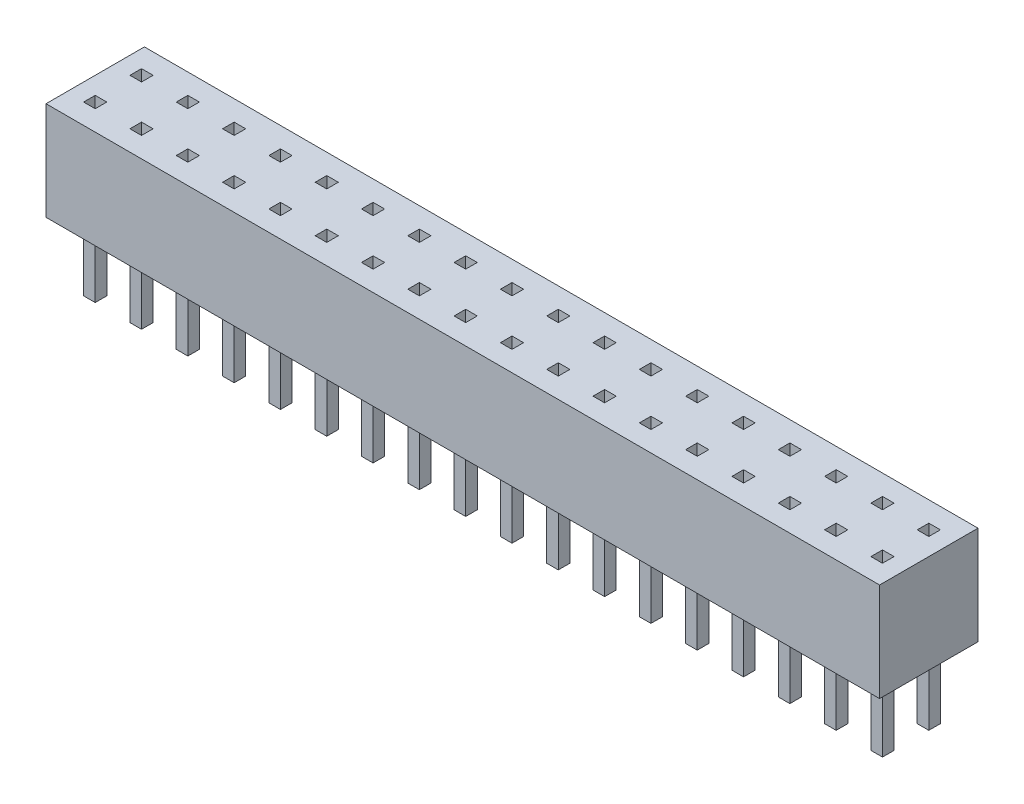
SolidWorks part; units mm, degrees
ref_plane "Front Plane" through (0, 0, 0) normal (0, 0, 1) x (1, 0, 0)
ref_plane "Top Plane" through (0, 0, 0) normal (0, 1, 0) x (1, 0, 0)
ref_plane "Right Plane" through (0, 0, 0) normal (1, 0, 0) x (0, 0, -1)
sketch "Sketch1" plane through (0, 0, 0) normal (0, 1, 0) x (1, 0, 0)
  line L1 (0, 0) -> (36, 0)
  line L2 (0, 0) -> (0, -4.25)
  line L3 (0, -4.25) -> (36, -4.25)
  line L4 (36, 0) -> (36, -4.25)
extrude "Boss-Extrude1" add sketch "Sketch1" along normal blind 4.25
sketch "Sketch3" plane through (0, 0, 0) normal (0, -1, 0) x (1, 0, 0)
  line L0 (2.75, 0.875) -> (3.25, 0.875)
  line L1 (0.75, 0.875) -> (1.25, 0.875)
  line L2 (0.75, 0.875) -> (0.75, 1.375)
  line L3 (0.75, 1.375) -> (1.25, 1.375)
  line L4 (1.25, 0.875) -> (1.25, 1.375)
  line L5 (2.75, 0.875) -> (2.75, 1.375)
  line L6 (2.75, 1.375) -> (3.25, 1.375)
  line L7 (3.25, 0.875) -> (3.25, 1.375)
  line L8 (4.75, 0.875) -> (5.25, 0.875)
  line L9 (4.75, 0.875) -> (4.75, 1.375)
  line L10 (4.75, 1.375) -> (5.25, 1.375)
  line L11 (5.25, 0.875) -> (5.25, 1.375)
  line L12 (6.75, 0.875) -> (7.25, 0.875)
  line L13 (6.75, 0.875) -> (6.75, 1.375)
  line L14 (6.75, 1.375) -> (7.25, 1.375)
  line L15 (7.25, 0.875) -> (7.25, 1.375)
  line L16 (8.75, 0.875) -> (9.25, 0.875)
  line L17 (8.75, 0.875) -> (8.75, 1.375)
  line L18 (8.75, 1.375) -> (9.25, 1.375)
  line L19 (9.25, 0.875) -> (9.25, 1.375)
  line L20 (10.75, 0.875) -> (11.25, 0.875)
  line L21 (10.75, 0.875) -> (10.75, 1.375)
  line L22 (10.75, 1.375) -> (11.25, 1.375)
  line L23 (11.25, 0.875) -> (11.25, 1.375)
  line L24 (12.75, 0.875) -> (13.25, 0.875)
  line L25 (12.75, 0.875) -> (12.75, 1.375)
  line L26 (12.75, 1.375) -> (13.25, 1.375)
  line L27 (13.25, 0.875) -> (13.25, 1.375)
  line L28 (14.75, 0.875) -> (15.25, 0.875)
  line L29 (14.75, 0.875) -> (14.75, 1.375)
  line L30 (14.75, 1.375) -> (15.25, 1.375)
  line L31 (15.25, 0.875) -> (15.25, 1.375)
  line L32 (16.75, 0.875) -> (17.25, 0.875)
  line L33 (16.75, 0.875) -> (16.75, 1.375)
  line L34 (16.75, 1.375) -> (17.25, 1.375)
  line L35 (17.25, 0.875) -> (17.25, 1.375)
  line L36 (18.75, 0.875) -> (19.25, 0.875)
  line L37 (18.75, 0.875) -> (18.75, 1.375)
  line L38 (18.75, 1.375) -> (19.25, 1.375)
  line L39 (19.25, 0.875) -> (19.25, 1.375)
  line L40 (20.75, 0.875) -> (21.25, 0.875)
  line L41 (20.75, 0.875) -> (20.75, 1.375)
  line L42 (20.75, 1.375) -> (21.25, 1.375)
  line L43 (21.25, 0.875) -> (21.25, 1.375)
  line L44 (22.75, 0.875) -> (23.25, 0.875)
  line L45 (22.75, 0.875) -> (22.75, 1.375)
  line L46 (22.75, 1.375) -> (23.25, 1.375)
  line L47 (23.25, 0.875) -> (23.25, 1.375)
  line L48 (24.75, 0.875) -> (25.25, 0.875)
  line L49 (24.75, 0.875) -> (24.75, 1.375)
  line L50 (24.75, 1.375) -> (25.25, 1.375)
  line L51 (25.25, 0.875) -> (25.25, 1.375)
  line L52 (26.75, 0.875) -> (27.25, 0.875)
  line L53 (26.75, 0.875) -> (26.75, 1.375)
  line L54 (26.75, 1.375) -> (27.25, 1.375)
  line L55 (27.25, 0.875) -> (27.25, 1.375)
  line L56 (28.75, 0.875) -> (29.25, 0.875)
  line L57 (28.75, 0.875) -> (28.75, 1.375)
  line L58 (28.75, 1.375) -> (29.25, 1.375)
  line L59 (29.25, 0.875) -> (29.25, 1.375)
  line L60 (30.75, 0.875) -> (31.25, 0.875)
  line L61 (30.75, 0.875) -> (30.75, 1.375)
  line L62 (30.75, 1.375) -> (31.25, 1.375)
  line L63 (31.25, 0.875) -> (31.25, 1.375)
  line L64 (32.75, 0.875) -> (33.25, 0.875)
  line L65 (32.75, 0.875) -> (32.75, 1.375)
  line L66 (32.75, 1.375) -> (33.25, 1.375)
  line L67 (33.25, 0.875) -> (33.25, 1.375)
  line L68 (34.75, 0.875) -> (35.25, 0.875)
  line L69 (34.75, 0.875) -> (34.75, 1.375)
  line L70 (34.75, 1.375) -> (35.25, 1.375)
  line L71 (35.25, 0.875) -> (35.25, 1.375)
  line L72 (0.75, 2.875) -> (1.25, 2.875)
  line L73 (0.75, 2.875) -> (0.75, 3.375)
  line L74 (0.75, 3.375) -> (1.25, 3.375)
  line L75 (1.25, 2.875) -> (1.25, 3.375)
  line L76 (2.75, 2.875) -> (3.25, 2.875)
  line L77 (2.75, 2.875) -> (2.75, 3.375)
  line L78 (2.75, 3.375) -> (3.25, 3.375)
  line L79 (3.25, 2.875) -> (3.25, 3.375)
  line L80 (4.75, 2.875) -> (5.25, 2.875)
  line L81 (4.75, 2.875) -> (4.75, 3.375)
  line L82 (4.75, 3.375) -> (5.25, 3.375)
  line L83 (5.25, 2.875) -> (5.25, 3.375)
  line L84 (6.75, 2.875) -> (7.25, 2.875)
  line L85 (6.75, 2.875) -> (6.75, 3.375)
  line L86 (6.75, 3.375) -> (7.25, 3.375)
  line L87 (7.25, 2.875) -> (7.25, 3.375)
  line L88 (8.75, 2.875) -> (9.25, 2.875)
  line L89 (8.75, 2.875) -> (8.75, 3.375)
  line L90 (8.75, 3.375) -> (9.25, 3.375)
  line L91 (9.25, 2.875) -> (9.25, 3.375)
  line L92 (10.75, 2.875) -> (11.25, 2.875)
  line L93 (10.75, 2.875) -> (10.75, 3.375)
  line L94 (10.75, 3.375) -> (11.25, 3.375)
  line L95 (11.25, 2.875) -> (11.25, 3.375)
  line L96 (12.75, 2.875) -> (13.25, 2.875)
  line L97 (12.75, 2.875) -> (12.75, 3.375)
  line L98 (12.75, 3.375) -> (13.25, 3.375)
  line L99 (13.25, 2.875) -> (13.25, 3.375)
  line L100 (14.75, 2.875) -> (15.25, 2.875)
  line L101 (14.75, 2.875) -> (14.75, 3.375)
  line L102 (14.75, 3.375) -> (15.25, 3.375)
  line L103 (15.25, 2.875) -> (15.25, 3.375)
  line L104 (16.75, 2.875) -> (17.25, 2.875)
  line L105 (16.75, 2.875) -> (16.75, 3.375)
  line L106 (16.75, 3.375) -> (17.25, 3.375)
  line L107 (17.25, 2.875) -> (17.25, 3.375)
  line L108 (18.75, 2.875) -> (19.25, 2.875)
  line L109 (18.75, 2.875) -> (18.75, 3.375)
  line L110 (18.75, 3.375) -> (19.25, 3.375)
  line L111 (19.25, 2.875) -> (19.25, 3.375)
  line L112 (20.75, 2.875) -> (21.25, 2.875)
  line L113 (20.75, 2.875) -> (20.75, 3.375)
  line L114 (20.75, 3.375) -> (21.25, 3.375)
  line L115 (21.25, 2.875) -> (21.25, 3.375)
  line L116 (22.75, 2.875) -> (23.25, 2.875)
  line L117 (22.75, 2.875) -> (22.75, 3.375)
  line L118 (22.75, 3.375) -> (23.25, 3.375)
  line L119 (23.25, 2.875) -> (23.25, 3.375)
  line L120 (24.75, 2.875) -> (25.25, 2.875)
  line L121 (24.75, 2.875) -> (24.75, 3.375)
  line L122 (24.75, 3.375) -> (25.25, 3.375)
  line L123 (25.25, 2.875) -> (25.25, 3.375)
  line L124 (26.75, 2.875) -> (27.25, 2.875)
  line L125 (26.75, 2.875) -> (26.75, 3.375)
  line L126 (26.75, 3.375) -> (27.25, 3.375)
  line L127 (27.25, 2.875) -> (27.25, 3.375)
  line L128 (28.75, 2.875) -> (29.25, 2.875)
  line L129 (28.75, 2.875) -> (28.75, 3.375)
  line L130 (28.75, 3.375) -> (29.25, 3.375)
  line L131 (29.25, 2.875) -> (29.25, 3.375)
  line L132 (30.75, 2.875) -> (31.25, 2.875)
  line L133 (30.75, 2.875) -> (30.75, 3.375)
  line L134 (30.75, 3.375) -> (31.25, 3.375)
  line L135 (31.25, 2.875) -> (31.25, 3.375)
  line L136 (32.75, 2.875) -> (33.25, 2.875)
  line L138 (32.75, 2.875) -> (32.75, 3.375)
  line L140 (32.75, 3.375) -> (33.25, 3.375)
  line L142 (33.25, 2.875) -> (33.25, 3.375)
  line L145 (34.75, 2.875) -> (35.25, 2.875)
  line L146 (34.75, 2.875) -> (34.75, 3.375)
  line L147 (34.75, 3.375) -> (35.25, 3.375)
  line L148 (35.25, 2.875) -> (35.25, 3.375)
  dimension "D2" = 2
  dimension "D1" = 18
extrude "Boss-Extrude2" add sketch "Sketch3" along normal blind 3
sketch "Sketch4" plane through (0, 4.25, 0) normal (0, 1, 0) x (-1, 0, 0)
  line L0 (-33.25, 0.875) -> (-32.75, 0.875)
  line L1 (-35.25, 0.875) -> (-34.75, 0.875)
  line L2 (-35.25, 0.875) -> (-35.25, 1.375)
  line L3 (-35.25, 1.375) -> (-34.75, 1.375)
  line L4 (-34.75, 0.875) -> (-34.75, 1.375)
  line L5 (-33.25, 0.875) -> (-33.25, 1.375)
  line L6 (-33.25, 1.375) -> (-32.75, 1.375)
  line L7 (-32.75, 0.875) -> (-32.75, 1.375)
  line L8 (-31.25, 0.875) -> (-30.75, 0.875)
  line L9 (-31.25, 0.875) -> (-31.25, 1.375)
  line L10 (-31.25, 1.375) -> (-30.75, 1.375)
  line L11 (-30.75, 0.875) -> (-30.75, 1.375)
  line L12 (-29.25, 0.875) -> (-28.75, 0.875)
  line L13 (-29.25, 0.875) -> (-29.25, 1.375)
  line L14 (-29.25, 1.375) -> (-28.75, 1.375)
  line L15 (-28.75, 0.875) -> (-28.75, 1.375)
  line L16 (-27.25, 0.875) -> (-26.75, 0.875)
  line L17 (-27.25, 0.875) -> (-27.25, 1.375)
  line L18 (-27.25, 1.375) -> (-26.75, 1.375)
  line L19 (-26.75, 0.875) -> (-26.75, 1.375)
  line L20 (-25.25, 0.875) -> (-24.75, 0.875)
  line L21 (-25.25, 0.875) -> (-25.25, 1.375)
  line L22 (-25.25, 1.375) -> (-24.75, 1.375)
  line L23 (-24.75, 0.875) -> (-24.75, 1.375)
  line L24 (-23.25, 0.875) -> (-22.75, 0.875)
  line L25 (-23.25, 0.875) -> (-23.25, 1.375)
  line L26 (-23.25, 1.375) -> (-22.75, 1.375)
  line L27 (-22.75, 0.875) -> (-22.75, 1.375)
  line L28 (-21.25, 0.875) -> (-20.75, 0.875)
  line L29 (-21.25, 0.875) -> (-21.25, 1.375)
  line L30 (-21.25, 1.375) -> (-20.75, 1.375)
  line L31 (-20.75, 0.875) -> (-20.75, 1.375)
  line L32 (-19.25, 0.875) -> (-18.75, 0.875)
  line L33 (-19.25, 0.875) -> (-19.25, 1.375)
  line L34 (-19.25, 1.375) -> (-18.75, 1.375)
  line L35 (-18.75, 0.875) -> (-18.75, 1.375)
  line L36 (-17.25, 0.875) -> (-16.75, 0.875)
  line L37 (-17.25, 0.875) -> (-17.25, 1.375)
  line L38 (-17.25, 1.375) -> (-16.75, 1.375)
  line L39 (-16.75, 0.875) -> (-16.75, 1.375)
  line L40 (-15.25, 0.875) -> (-14.75, 0.875)
  line L41 (-15.25, 0.875) -> (-15.25, 1.375)
  line L42 (-15.25, 1.375) -> (-14.75, 1.375)
  line L43 (-14.75, 0.875) -> (-14.75, 1.375)
  line L44 (-13.25, 0.875) -> (-12.75, 0.875)
  line L45 (-13.25, 0.875) -> (-13.25, 1.375)
  line L46 (-13.25, 1.375) -> (-12.75, 1.375)
  line L47 (-12.75, 0.875) -> (-12.75, 1.375)
  line L48 (-11.25, 0.875) -> (-10.75, 0.875)
  line L49 (-11.25, 0.875) -> (-11.25, 1.375)
  line L50 (-11.25, 1.375) -> (-10.75, 1.375)
  line L51 (-10.75, 0.875) -> (-10.75, 1.375)
  line L52 (-9.25, 0.875) -> (-8.75, 0.875)
  line L53 (-9.25, 0.875) -> (-9.25, 1.375)
  line L54 (-9.25, 1.375) -> (-8.75, 1.375)
  line L55 (-8.75, 0.875) -> (-8.75, 1.375)
  line L56 (-7.25, 0.875) -> (-6.75, 0.875)
  line L57 (-7.25, 0.875) -> (-7.25, 1.375)
  line L58 (-7.25, 1.375) -> (-6.75, 1.375)
  line L59 (-6.75, 0.875) -> (-6.75, 1.375)
  line L60 (-5.25, 0.875) -> (-4.75, 0.875)
  line L61 (-5.25, 0.875) -> (-5.25, 1.375)
  line L62 (-5.25, 1.375) -> (-4.75, 1.375)
  line L63 (-4.75, 0.875) -> (-4.75, 1.375)
  line L64 (-3.25, 0.875) -> (-2.75, 0.875)
  line L65 (-3.25, 0.875) -> (-3.25, 1.375)
  line L66 (-3.25, 1.375) -> (-2.75, 1.375)
  line L67 (-2.75, 0.875) -> (-2.75, 1.375)
  line L68 (-1.25, 0.875) -> (-0.75, 0.875)
  line L69 (-1.25, 0.875) -> (-1.25, 1.375)
  line L70 (-1.25, 1.375) -> (-0.75, 1.375)
  line L71 (-0.75, 0.875) -> (-0.75, 1.375)
  line L72 (-35.25, 2.875) -> (-34.75, 2.875)
  line L73 (-35.25, 2.875) -> (-35.25, 3.375)
  line L74 (-35.25, 3.375) -> (-34.75, 3.375)
  line L75 (-34.75, 2.875) -> (-34.75, 3.375)
  line L76 (-33.25, 2.875) -> (-32.75, 2.875)
  line L77 (-33.25, 2.875) -> (-33.25, 3.375)
  line L78 (-33.25, 3.375) -> (-32.75, 3.375)
  line L79 (-32.75, 2.875) -> (-32.75, 3.375)
  line L80 (-31.25, 2.875) -> (-30.75, 2.875)
  line L81 (-31.25, 2.875) -> (-31.25, 3.375)
  line L82 (-31.25, 3.375) -> (-30.75, 3.375)
  line L83 (-30.75, 2.875) -> (-30.75, 3.375)
  line L84 (-29.25, 2.875) -> (-28.75, 2.875)
  line L85 (-29.25, 2.875) -> (-29.25, 3.375)
  line L86 (-29.25, 3.375) -> (-28.75, 3.375)
  line L87 (-28.75, 2.875) -> (-28.75, 3.375)
  line L88 (-27.25, 2.875) -> (-26.75, 2.875)
  line L89 (-27.25, 2.875) -> (-27.25, 3.375)
  line L90 (-27.25, 3.375) -> (-26.75, 3.375)
  line L91 (-26.75, 2.875) -> (-26.75, 3.375)
  line L92 (-25.25, 2.875) -> (-24.75, 2.875)
  line L93 (-25.25, 2.875) -> (-25.25, 3.375)
  line L94 (-25.25, 3.375) -> (-24.75, 3.375)
  line L95 (-24.75, 2.875) -> (-24.75, 3.375)
  line L96 (-23.25, 2.875) -> (-22.75, 2.875)
  line L97 (-23.25, 2.875) -> (-23.25, 3.375)
  line L98 (-23.25, 3.375) -> (-22.75, 3.375)
  line L99 (-22.75, 2.875) -> (-22.75, 3.375)
  line L100 (-21.25, 2.875) -> (-20.75, 2.875)
  line L101 (-21.25, 2.875) -> (-21.25, 3.375)
  line L102 (-21.25, 3.375) -> (-20.75, 3.375)
  line L103 (-20.75, 2.875) -> (-20.75, 3.375)
  line L104 (-19.25, 2.875) -> (-18.75, 2.875)
  line L105 (-19.25, 2.875) -> (-19.25, 3.375)
  line L106 (-19.25, 3.375) -> (-18.75, 3.375)
  line L107 (-18.75, 2.875) -> (-18.75, 3.375)
  line L108 (-17.25, 2.875) -> (-16.75, 2.875)
  line L109 (-17.25, 2.875) -> (-17.25, 3.375)
  line L110 (-17.25, 3.375) -> (-16.75, 3.375)
  line L111 (-16.75, 2.875) -> (-16.75, 3.375)
  line L112 (-15.25, 2.875) -> (-14.75, 2.875)
  line L113 (-15.25, 2.875) -> (-15.25, 3.375)
  line L114 (-15.25, 3.375) -> (-14.75, 3.375)
  line L115 (-14.75, 2.875) -> (-14.75, 3.375)
  line L116 (-13.25, 2.875) -> (-12.75, 2.875)
  line L117 (-13.25, 2.875) -> (-13.25, 3.375)
  line L118 (-13.25, 3.375) -> (-12.75, 3.375)
  line L119 (-12.75, 2.875) -> (-12.75, 3.375)
  line L120 (-11.25, 2.875) -> (-10.75, 2.875)
  line L121 (-11.25, 2.875) -> (-11.25, 3.375)
  line L122 (-11.25, 3.375) -> (-10.75, 3.375)
  line L123 (-10.75, 2.875) -> (-10.75, 3.375)
  line L124 (-9.25, 2.875) -> (-8.75, 2.875)
  line L125 (-9.25, 2.875) -> (-9.25, 3.375)
  line L126 (-9.25, 3.375) -> (-8.75, 3.375)
  line L127 (-8.75, 2.875) -> (-8.75, 3.375)
  line L128 (-7.25, 2.875) -> (-6.75, 2.875)
  line L129 (-7.25, 2.875) -> (-7.25, 3.375)
  line L130 (-7.25, 3.375) -> (-6.75, 3.375)
  line L131 (-6.75, 2.875) -> (-6.75, 3.375)
  line L132 (-5.25, 2.875) -> (-4.75, 2.875)
  line L133 (-5.25, 2.875) -> (-5.25, 3.375)
  line L134 (-5.25, 3.375) -> (-4.75, 3.375)
  line L135 (-4.75, 2.875) -> (-4.75, 3.375)
  line L137 (-3.25, 2.875) -> (-2.75, 2.875)
  line L138 (-3.25, 2.875) -> (-3.25, 3.375)
  line L139 (-3.25, 3.375) -> (-2.75, 3.375)
  line L140 (-2.75, 2.875) -> (-2.75, 3.375)
  line L141 (-1.25, 2.875) -> (-0.75, 2.875)
  line L142 (-1.25, 2.875) -> (-1.25, 3.375)
  line L143 (-1.25, 3.375) -> (-0.75, 3.375)
  line L144 (-0.75, 2.875) -> (-0.75, 3.375)
  dimension "D2" = 2
  dimension "D1" = 18
extrude "Cut-Extrude1" cut sketch "Sketch4" against normal blind 4
